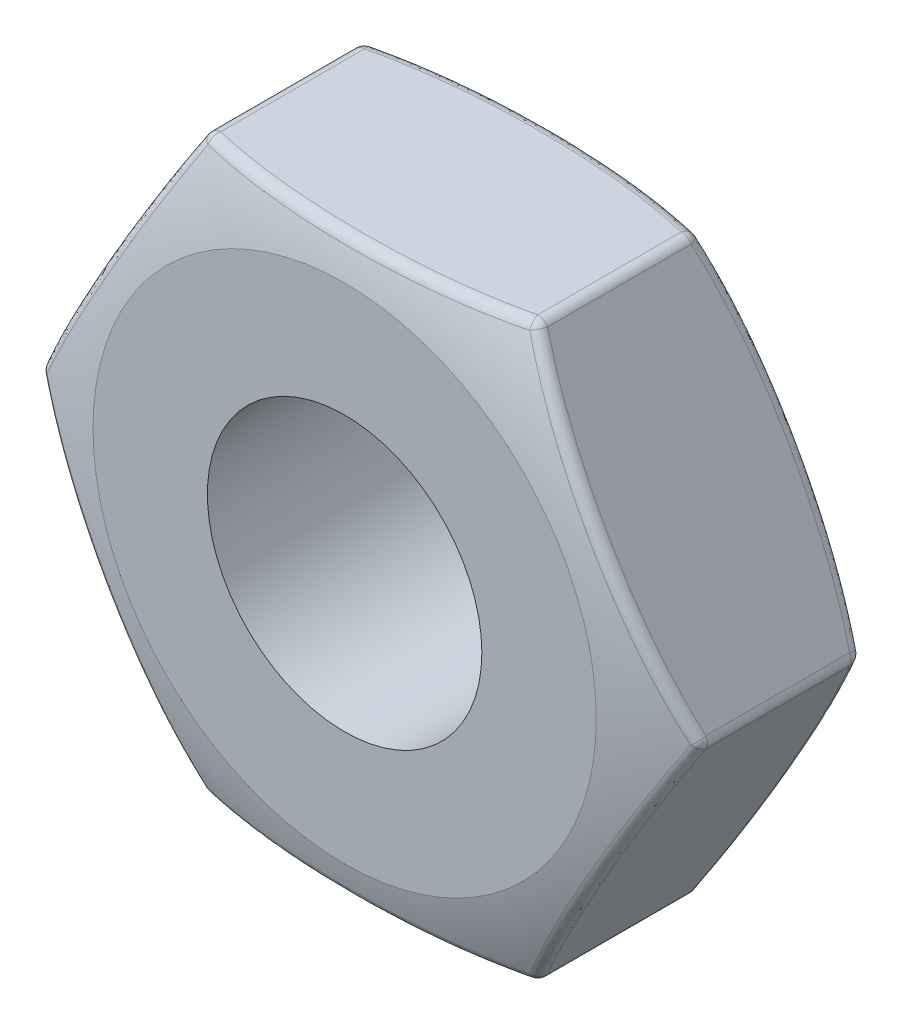
SolidWorks part; units mm, degrees
ref_plane "Front Plane" through (0, 0, 0) normal (0, 0, 1) x (1, 0, 0)
ref_plane "Top Plane" through (0, 0, 0) normal (0, 1, 0) x (1, 0, 0)
ref_plane "Right Plane" through (0, 0, 0) normal (1, 0, 0) x (0, 0, -1)
sketch "Sketch1" plane through (0, 0, 0) normal (0, 0, 1) x (1, 0, 0)
  line L1 (2.8868, 0) -> (1.4434, 2.5)
  line L2 (1.4434, 2.5) -> (-1.4434, 2.5)
  line L3 (-1.4434, 2.5) -> (-2.8868, 0)
  line L4 (-2.8868, 0) -> (-1.4434, -2.5)
  line L5 (-1.4434, -2.5) -> (1.4434, -2.5)
  line L6 (1.4434, -2.5) -> (2.8868, 0)
  circle A0 centre (0, 0) radius 2.5 construction
  dimension "D1" = 5
extrude "Extrude1" add sketch "Sketch1" along normal blind 1.86
sketch "Sketch2" plane through (0, 0, 0) normal (1, 0, 0) x (0, 0, -1)
  line L0 (1.0118, 0) -> (-3.858, 0) construction
  line L1 (0, 2.5) -> (0, 0) construction
  line L3 (-0.5, 3.3) -> (0.4733, 3.3)
  line L4 (0.4733, 3.3) -> (0.4733, 2.2)
  line L5 (0.4733, 2.2) -> (0, 2.2)
  line L6 (-1.86, 2.5) -> (-1.86, 0) construction
  line L7 (-1.36, 3.3) -> (-2.8363, 3.3)
  line L8 (-2.8363, 3.3) -> (-2.8363, 2.2)
  line L9 (-2.8363, 2.2) -> (-1.86, 2.2)
  arc A0 (0, 2.2) -> (-0.5, 3.3) centre (-2.9251, 1.534) ccw
  arc A1 (-1.36, 3.3) -> (-1.86, 2.2) centre (1.0651, 1.534) ccw
  dimension "D4" = 3
  dimension "D5" = 3.3
  dimension "D8" = 3
  dimension "D1" = 2.2
  dimension "D2" = 3.3
  dimension "D3" = 0.5
  dimension "D6" = 2.2
  dimension "D7" = 0.5
revolve "Cut-Revolve1" cut sketch "Sketch2" angle 360 about L0
sketch "Sketch3" plane through (0, 0, 1.86) normal (0, 0, 1) x (1, 0, 0)
  circle A0 centre (0, 0) radius 1.2
  dimension "D1" = 2.4
extrude "Cut-Extrude1" cut sketch "Sketch3" against normal blind 12.5
fillet "Fillet1" radius 0.1 6 edges at (-1.4434, 2.5, 0.93) (-2.8868, 0, 0.93) (-1.4434, -2.5, 0.93) (1.4434, -2.5, 0.93) (2.8868, 0, 0.93) (1.4434, 2.5, 0.93)
fillet "Fillet2" radius 0.1 24 edges at (-2.8708, 0.0099, 0.2394) (-2.4399, 0.7739, 0.1059) (-1.4268, 2.4911, 0.2394) (-0.9739, 2.5, 5.6964) (1.444, 2.4812, 0.2394) (1.8902, 1.7261, 0.1059) (2.8708, -0.0099, 0.2394) (2.4399, -0.7739, 0.1059) (1.4268, -2.4911, 0.2394) (0.9739, -2.5, 5.6964) (-1.444, -2.4812, 0.2394) (-1.4268, -2.4911, 1.6206) (-0.9739, -2.5, -3.8364) (1.444, -2.4812, 1.6206) (1.8902, -1.7261, 1.7541) (2.8708, 0.0099, 1.6206) (2.4399, 0.7739, 1.7541) (1.4268, 2.4911, 1.6206) (0.9739, 2.5, -3.8364) (-1.444, 2.4812, 1.6206) (-1.8902, 1.7261, 1.7541) (-2.8708, -0.0099, 1.6206) (-1.8902, -1.7261, 0.1059) (-2.4399, -0.7739, 1.7541)
